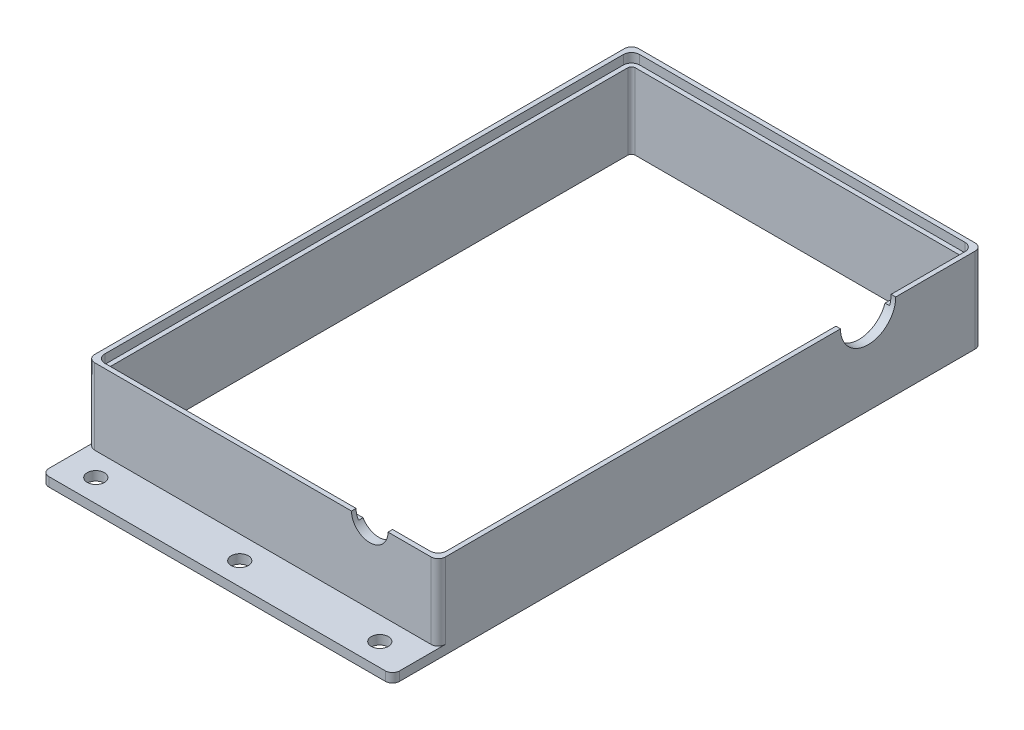
SolidWorks part; units mm, degrees
ref_plane "Front Plane" through (0, 0, 0) normal (0, 0, 1) x (1, 0, 0)
ref_plane "Top Plane" through (0, 0, 0) normal (0, 1, 0) x (1, 0, 0)
ref_plane "Right Plane" through (0, 0, 0) normal (1, 0, 0) x (0, 0, -1)
sketch "Sketch1" plane through (0, 0, 0) normal (0, 1, 0) x (1, 0, 0)
  line L12 (-48.7855, 75.6728) -> (-48.7855, -75.6728)
  line L23 (-46.2455, 73.1328) -> (46.2455, 73.1328)
  line L27 (-48.7855, -75.6728) -> (48.7855, -75.6728)
  line L28 (-46.2455, 73.1328) -> (-46.2455, -73.1328)
  line L43 (-48.7855, 75.6728) -> (48.7855, 75.6728)
  line L48 (48.7855, 75.6728) -> (48.7855, -75.6728)
  line L49 (-46.2455, -73.1328) -> (46.2455, -73.1328)
  line L50 (46.2455, 73.1328) -> (46.2455, -73.1328)
  line L51 (-46.2455, 73.1328) -> (46.2455, -73.1328) construction
  line L52 (-46.2455, -73.1328) -> (46.2455, 73.1328) construction
  point P0 (-48.7855, 0)
  point P1 (0, 75.6728)
  point P4 (0, 0)
  dimension "D3" = 2.54
  dimension "D19" = 97.5711
  dimension "D4" = 2.54
  dimension "D2" = 151.3455
extrude "Boss-Extrude1" add sketch "Sketch1" along normal blind 23.619
sketch "Sketch2" plane through (0, 0, 0) normal (0, -1, 0) x (1, 0, 0)
  line L0 (-48.7855, 75.6728) -> (-48.7855, 88.3973)
  line L1 (-48.7855, 88.3973) -> (48.7855, 88.3973)
  line L2 (48.7855, 88.3973) -> (48.7855, 75.6728)
  line L4 (48.7855, -75.6728) -> (48.7855, 75.6728)
  line L5 (48.7855, 75.6728) -> (-48.7855, 75.6728)
  line L6 (-48.7855, 75.6728) -> (-48.7855, -75.6728)
  line L7 (-48.7855, -75.6728) -> (48.7855, -75.6728)
  line L9 (48.7855, 75.6728) -> (-48.7855, 75.6728)
  dimension "D1" = 0
extrude "Boss-Extrude2" add sketch "Sketch2" against normal blind 2.54
fillet "Fillet1" radius 2 6 edges at (-48.7855, 11.8095, -75.6728) (48.7855, 11.8095, -75.6728) (-48.7855, 13.0795, 75.6728) (48.7855, 13.0795, 75.6728) (48.7855, 1.27, 88.3973) (-48.7855, 1.27, 88.3973)
fillet "Fillet2" radius 1 4 edges at (46.2455, 11.8095, 73.1328) (46.2455, 11.8095, -73.1328) (-46.2455, 11.8095, -73.1328) (-46.2455, 11.8095, 73.1328)
sketch "Sketch3" plane through (0, 2.54, 0) normal (0, 1, 0) x (1, 0, 0)
  point P0 (-40.0459, -82.1012)
  point P2 (38.9577, -82.1012)
  point P4 (0, -82.1012)
hole_wizard "3/16 (0.1875) Diameter Hole1" positions "Sketch3" profile "Sketch4" hole size "3/16" standard "ANSI Inch"
sketch "Sketch4" plane through (-40.0459, 2.54, 82.1012) normal (1, 0, 0) x (0, 0, 1)
  line L0 (0, 0) -> (0, 21.4968)
  line L1 (0, 21.4968) -> (2.3812, 20.066)
  line L2 (2.3812, 20.066) -> (2.3812, 0)
  line L5 (2.3812, 0) -> (0, 0)
  line L10 (0, 21.4968) -> (-2.3812, 20.066) construction
  line L11 (0, -6.35) -> (0, 107.95) construction
  dimension "Hole Dia." = 4.7625
  dimension "Hole Depth" = 20.066
  dimension "Drill Angle" = 118
sketch "Sketch5" plane through (0, 23.619, 0) normal (0, 1, 0) x (1, 0, 0)
  line L0 (-46.2455, 72.1328) -> (-46.2455, -72.1328) construction
  line L1 (-46.2455, 72.1328) -> (-46.2455, -72.1328)
  line L2 (45.2455, 73.1328) -> (-45.2455, 73.1328) construction
  line L3 (46.2455, -72.1328) -> (46.2455, 72.1328) construction
  line L4 (-45.2455, -73.1328) -> (45.2455, -73.1328) construction
  line L5 (45.2455, 73.1328) -> (-45.2455, 73.1328)
  line L6 (46.2455, -72.1328) -> (46.2455, 72.1328)
  line L7 (-45.2455, -73.1328) -> (45.2455, -73.1328)
  line L8 (-45.2455, -74.4028) -> (45.2455, -74.4028)
  line L9 (47.5155, -72.1328) -> (47.5155, 72.1328)
  line L10 (45.2455, 74.4028) -> (-45.2455, 74.4028)
  line L11 (-47.5155, 72.1328) -> (-47.5155, -72.1328)
  arc A0 (-46.2455, -72.1328) -> (-45.2455, -73.1328) centre (-45.2455, -72.1328) ccw construction
  arc A1 (45.2455, -73.1328) -> (46.2455, -72.1328) centre (45.2455, -72.1328) ccw construction
  arc A2 (46.2455, 72.1328) -> (45.2455, 73.1328) centre (45.2455, 72.1328) ccw construction
  arc A3 (-45.2455, 73.1328) -> (-46.2455, 72.1328) centre (-45.2455, 72.1328) ccw construction
  arc A4 (-46.2455, -72.1328) -> (-45.2455, -73.1328) centre (-45.2455, -72.1328) ccw
  arc A5 (45.2455, -73.1328) -> (46.2455, -72.1328) centre (45.2455, -72.1328) ccw
  arc A6 (46.2455, 72.1328) -> (45.2455, 73.1328) centre (45.2455, 72.1328) ccw
  arc A7 (-45.2455, 73.1328) -> (-46.2455, 72.1328) centre (-45.2455, 72.1328) ccw
  arc A8 (45.2455, -74.4028) -> (47.5155, -72.1328) centre (45.2455, -72.1328) ccw
  arc A9 (47.5155, 72.1328) -> (45.2455, 74.4028) centre (45.2455, 72.1328) ccw
  arc A10 (-45.2455, 74.4028) -> (-47.5155, 72.1328) centre (-45.2455, 72.1328) ccw
  arc A11 (-47.5155, -72.1328) -> (-45.2455, -74.4028) centre (-45.2455, -72.1328) ccw
  dimension "D1" = 1.27
extrude "Cut-Extrude1" cut sketch "Sketch5" against normal blind 2.54
sketch "Sketch8" plane through (48.7855, 0, 0) normal (1, 0, 0) x (0, 0, -1)
  line L0 (-73.6728, 23.619) -> (73.6728, 23.619) construction
  line L1 (75.6728, 23.619) -> (75.6728, 0) construction
  circle A0 centre (43.9228, 23.619) radius 7.6835
  point P6 (0, 0)
  dimension "D1" = 15.367
  dimension "D2" = 31.75
extrude "Cut-Extrude2" cut sketch "Sketch8" against normal up to next
sketch "Sketch9" plane through (0, 0, 75.6728) normal (0, 0, 1) x (1, 0, 0)
  line L0 (-46.7855, 23.619) -> (46.7855, 23.619) construction
  line L1 (48.7855, 23.619) -> (48.7855, 2.54) construction
  circle A0 centre (29.7355, 23.619) radius 5.08
  dimension "D2" = 10.16
  dimension "D1" = 19.05
extrude "Cut-Extrude3" cut sketch "Sketch9" against normal up to next
